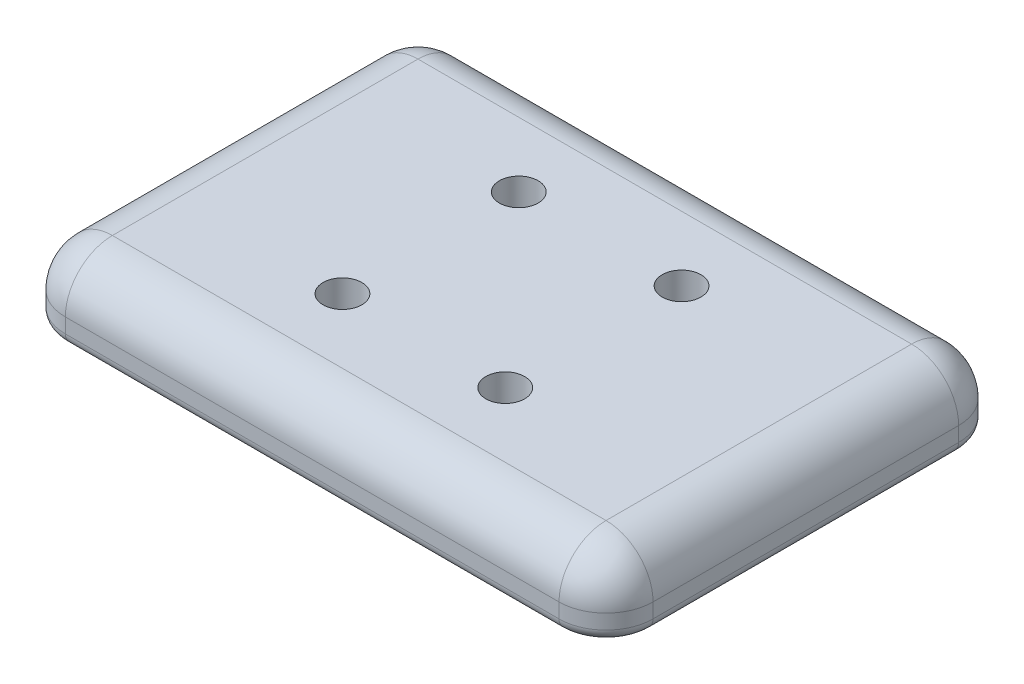
SolidWorks part; units mm, degrees
material "6061 Alloy"
ref_plane "Front Plane" through (0, 0, 0) normal (0, 0, 1) x (1, 0, 0)
ref_plane "Top Plane" through (0, 0, 0) normal (0, 1, 0) x (1, 0, 0)
ref_plane "Right Plane" through (0, 0, 0) normal (1, 0, 0) x (0, 0, -1)
sketch "Sketch1" plane through (0, 0, 0) normal (0, 1, 0) x (1, 0, 0)
  line L1 (0, 0) -> (100, 0)
  line L2 (0, 0) -> (0, -68)
  line L3 (0, -68) -> (100, -68)
  line L4 (100, 0) -> (100, -68)
  dimension "D1" = 100
  dimension "D2" = 68
extrude "Boss-Extrude1" add sketch "Sketch1" along normal blind 12.5
hole_wizard "CBORE for M6 Hex Head Cap Screw1" positions "3DSketch1" profile "Sketch2" counterbore size "M6" standard "ISO" end condition through all
sketch3d "3DSketch1"
  line L0 (36.15, 0, 49) -> (63.85, 0, 49) construction
  line L5 (36.15, 0, 49) -> (36.15, 0, 19) construction
  line L8 (0, 0, 0) -> (0, 0, 68) construction
  line L9 (36.15, 0, 19) -> (63.85, 0, 19) construction
  line L10 (63.85, 0, 19) -> (63.85, 0, 49) construction
  line L13 (100, 0, 68) -> (100, 0, 0) construction
  line L14 (0, 0, 68) -> (100, 0, 68) construction
  line L15 (100, 0, 0) -> (0, 0, 0) construction
  point P0 (36.15, 0, 49)
  point P2 (36.15, 0, 19)
  point P4 (63.85, 0, 49)
  point P6 (63.85, 0, 19)
  dimension "D1" = 36.15
  dimension "D2" = 36.15
  dimension "D3" = 19
  dimension "D4" = 19
sketch "Sketch2" plane through (36.15, 0, 49) normal (1, 0, 0) x (0, 0, -1)
  line L0 (0, 0) -> (0, 12.5)
  line L1 (0, 12.5) -> (3.3, 12.5)
  line L3 (3.3, 12.5) -> (3.3, 6)
  line L4 (3.3, 6) -> (7.2735, 6)
  line L5 (7.2735, 6) -> (7.2735, 0)
  line L7 (7.2735, 0) -> (0, 0)
  line L11 (0, -6.35) -> (0, 107.95) construction
  dimension "Thru Hole Dia." = 6.6
  dimension "Thru Hole Depth" = 12.5
  dimension "C'Bore Dia." = 14.547
  dimension "C'Bore Depth" = 6
fillet "Fillet1" radius 8 8 edges at (100, 6.25, 68) (100, 12.5, 34) (0, 6.25, 0) (50, 12.5, 0) (0, 6.25, 68) (100, 6.25, 0) (50, 12.5, 68) (0, 12.5, 34)
fillet "Fillet2" radius 2 8 edges at (2.3431, 0, 65.6569) (0, 0, 34) (2.3431, 0, 2.3431) (50, 0, 0) (97.6569, 0, 2.3431) (100, 0, 34) (97.6569, 0, 65.6569) (50, 0, 68)
